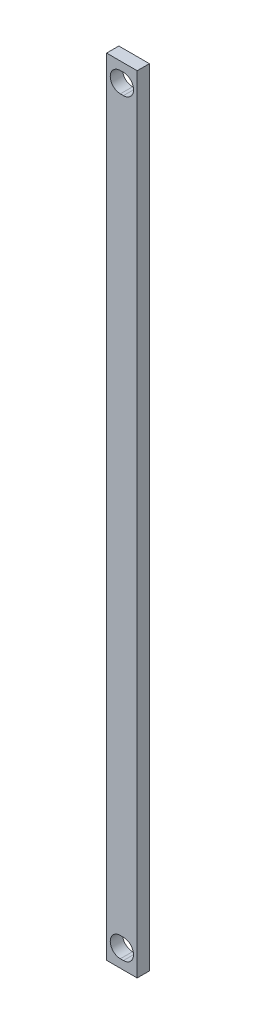
SolidWorks part; units mm, degrees
ref_plane "Front Plane" through (0, 0, 0) normal (0, 0, 1) x (1, 0, 0)
ref_plane "Top Plane" through (0, 0, 0) normal (0, 1, 0) x (1, 0, 0)
ref_plane "Right Plane" through (0, 0, 0) normal (1, 0, 0) x (0, 0, -1)
sketch "Sketch1" plane through (0, 0, 0) normal (0, 0, 1) x (1, 0, 0)
  line L0 (0, 64.25) -> (0, -64.25) construction
  line L1 (-2.5, 64.25) -> (2.5, 64.25)
  line L2 (-2.5, 64.25) -> (-2.5, -64.25)
  line L3 (-2.5, -64.25) -> (2.5, -64.25)
  line L4 (2.5, 64.25) -> (2.5, -64.25)
  line L5 (-2.5, 64.25) -> (2.5, -64.25) construction
  line L6 (-2.5, -64.25) -> (2.5, 64.25) construction
  line L7 (-2.5, 61.25) -> (2.5, 61.25) construction
  line L8 (-2.5, -61.25) -> (2.5, -61.25) construction
  line L9 (-0.254, -61.25) -> (0.254, -61.25) construction
  line L11 (-0.254, -59.6) -> (0.254, -59.6)
  line L12 (-0.254, -62.9) -> (0.254, -62.9)
  line L13 (-0.254, 61.25) -> (0.254, 61.25) construction
  line L14 (-0.254, 62.9) -> (0.254, 62.9)
  line L15 (-0.254, 59.6) -> (0.254, 59.6)
  arc A0 (-0.254, -59.6) -> (-0.254, -62.9) centre (-0.254, -61.25) ccw
  arc A1 (0.254, -62.9) -> (0.254, -59.6) centre (0.254, -61.25) ccw
  arc A2 (-0.254, 62.9) -> (-0.254, 59.6) centre (-0.254, 61.25) ccw
  arc A3 (0.254, 59.6) -> (0.254, 62.9) centre (0.254, 61.25) ccw
  point P0 (0, 0)
  point P18 (0, -61.25)
  point P24 (0, 61.25)
  dimension "D6" = 1.65
  dimension "D7" = 1.65
  dimension "D3" = 0.508
  dimension "D8" = 0.508
  dimension "D1" = 128.5
  dimension "D2" = 5
  dimension "D4" = 3
  dimension "D5" = 3
extrude "Boss-Extrude1" add sketch "Sketch1" along normal blind 2
